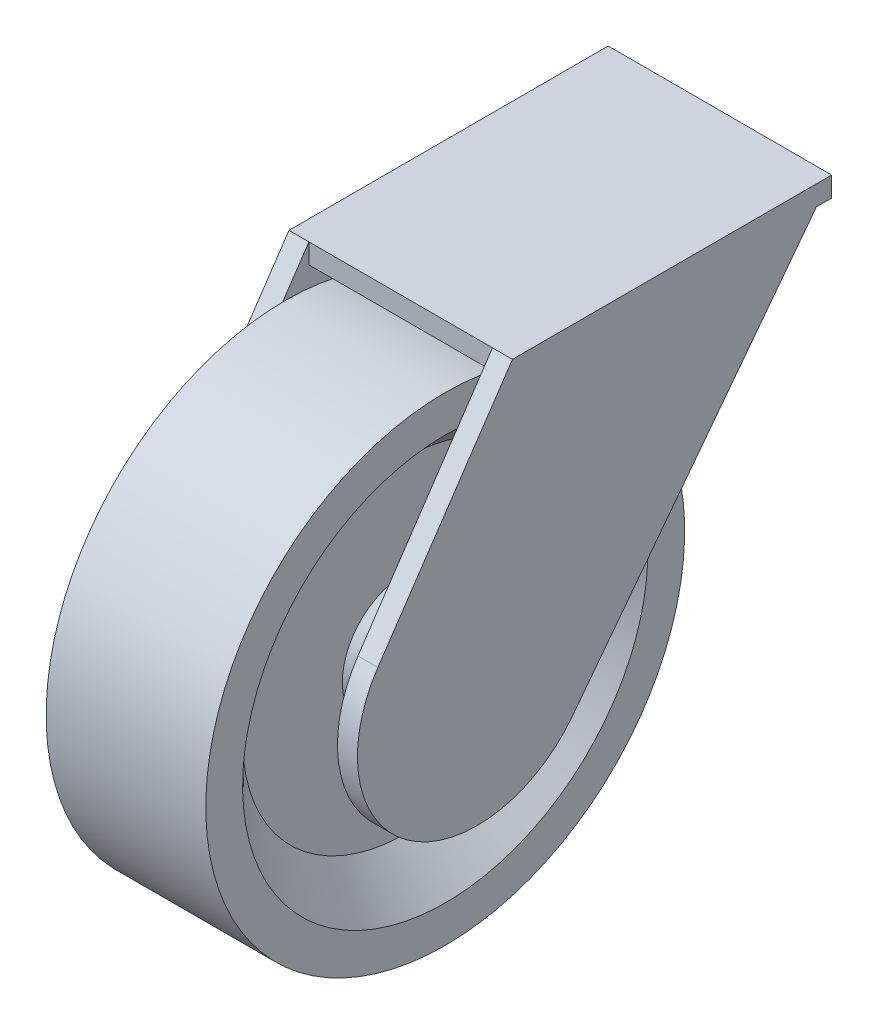
SolidWorks part; units mm, degrees
ref_plane "Front Plane" through (0, 0, 0) normal (0, 0, 1) x (1, 0, 0)
ref_plane "Top Plane" through (0, 0, 0) normal (0, 1, 0) x (1, 0, 0)
ref_plane "Right Plane" through (0, 0, 0) normal (1, 0, 0) x (0, 0, -1)
sketch "Sketch1" plane through (0, 0, 0) normal (0, 0, 1) x (1, 0, 0)
  line L0 (-40, 60) -> (0, 60)
  line L1 (0, 60) -> (0, 50.7735)
  line L2 (0, 50.7735) -> (-10, 40.7735)
  line L3 (-10, 40.7735) -> (-10, 15.7735)
  line L4 (-10, 15.7735) -> (0, 10)
  line L5 (0, 10) -> (0, 0)
  line L6 (0, 0) -> (-40, 0)
  line L8 (-20, 60) -> (-20, -29.9521) construction
  line L9 (-40, 10) -> (-40, 0)
  line L10 (-30, 15.7735) -> (-40, 10)
  line L11 (-30, 40.7735) -> (-30, 15.7735)
  line L12 (-40, 50.7735) -> (-30, 40.7735)
  line L13 (-40, 60) -> (-40, 50.7735)
  dimension "D1" = 60
  dimension "D2" = 40
  dimension "D4" = 135
  dimension "D5" = 120
  dimension "D6" = 25
  dimension "D7" = 10
revolve "Revolve1" add sketch "Sketch1" angle 360 about L6
sketch "Sketch3" plane through (0, 0, 0) normal (1, 0, 0) x (0, 0, -1)
  circle A0 centre (0, 0) radius 7.5
  dimension "D1" = 15
extrude "Boss-Extrude1" add sketch "Sketch3" along normal blind 8
sketch "Sketch4" plane through (8, 0, 0) normal (1, 0, 0) x (0, 0, -1)
  line L0 (8.8458, 66.7734) -> (88.8458, 66.7734)
  line L1 (88.8458, 66.7734) -> (23.8284, -18.2266)
  line L2 (-24.8727, 16.7734) -> (8.8458, 66.7734)
  arc A0 (23.8284, -18.2266) -> (-24.8727, 16.7734) centre (0, 0) cw
  circle A1 centre (0, 0) radius 7.5 construction
  dimension "D4" = 30
  dimension "D1" = 80
  dimension "D2" = 85
  dimension "D3" = 50
extrude "Boss-Extrude2" add sketch "Sketch4" against normal blind 5
ref_plane "Plane1" through (-20, 0, 0) normal (1, 0, 0) x (0, 0, -1)
mirror "Mirror1" about plane through (-20, 0, 0) normal (1, 0, 0) of "Boss-Extrude2", "Boss-Extrude1"
sketch "Sketch5" plane through (0, 66.7734, 0) normal (0, 1, 0) x (1, 0, 0)
  line L1 (-48, 88.8458) -> (8, 88.8458)
  line L2 (-48, 88.8458) -> (-48, 8.8458)
  line L3 (-48, 8.8458) -> (8, 8.8458)
  line L4 (8, 88.8458) -> (8, 8.8458)
extrude "Boss-Extrude3" add sketch "Sketch5" against normal blind 5
